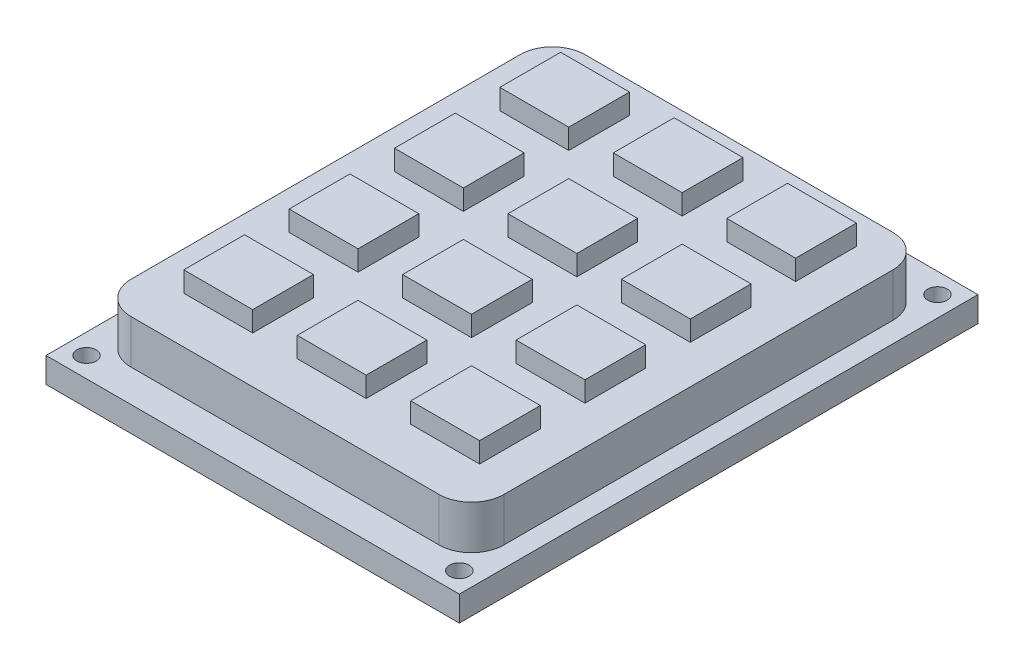
SolidWorks part; units mm, degrees
ref_plane "Front" through (0, 0, 0) normal (0, 0, 1) x (1, 0, 0)
ref_plane "Top" through (0, 0, 0) normal (0, 1, 0) x (1, 0, 0)
ref_plane "Right" through (0, 0, 0) normal (1, 0, 0) x (0, 0, -1)
sketch "Sketch1" plane through (0, 0, 0) normal (0, 1, 0) x (1, 0, 0)
  line L5 (25.5, -32) -> (-25.5, -32)
  line L6 (25.5, -32) -> (25.5, 32)
  line L7 (25.5, 32) -> (-25.5, 32)
  line L8 (-25.5, -32) -> (-25.5, 32)
  line L9 (0, 32) -> (0, -32) construction
  line L10 (25.5, 0) -> (-25.5, 0) construction
extrude "Boss-Extrude1" add sketch "Sketch1" along normal blind 3.1
sketch "Sketch2" plane through (0, 3.1, 0) normal (0, 1, 0) x (1, 0, 0)
  circle A0 centre (-23, 29.5) radius 1.2
  circle A1 centre (23, 29.5) radius 1.2
  circle A2 centre (23, -29.5) radius 1.2
  circle A3 centre (-23, -29.5) radius 1.2
extrude "Cut-Extrude1" cut sketch "Sketch2" against normal blind 3.1
sketch "Sketch3" plane through (0, 3.1, 0) normal (0, 1, 0) x (1, 0, 0)
  line L0 (-19, 28) -> (19, 28)
  line L4 (-23, 24) -> (-23, -24)
  line L14 (-19, -28) -> (19, -28)
  line L16 (23, -24) -> (23, 24)
  arc A0 (-19, -28) -> (-23, -24) centre (-19, -24) cw
  arc A1 (19, -28) -> (23, -24) centre (19, -24) ccw
  arc A2 (-19, 28) -> (-23, 24) centre (-19, 24) ccw
  arc A3 (23, 24) -> (19, 28) centre (19, 24) ccw
extrude "Boss-Extrude2" add sketch "Sketch3" along normal blind 5.4
sketch "Sketch4" plane through (0, 8.5, 0) normal (0, 1, 0) x (1, 0, 0)
  line L4 (-9.75, 16.75) -> (-18.25, 16.75)
  line L5 (-9.75, 16.75) -> (-9.75, 24.25)
  line L6 (-9.75, 24.25) -> (-18.25, 24.25)
  line L7 (-18.25, 16.75) -> (-18.25, 24.25)
  line L12 (4.25, 16.75) -> (-4.25, 16.75)
  line L13 (4.25, 16.75) -> (4.25, 24.25)
  line L14 (4.25, 24.25) -> (-4.25, 24.25)
  line L15 (-4.25, 16.75) -> (-4.25, 24.25)
  line L18 (-9.75, -22.25) -> (-18.25, -22.25)
  line L19 (-9.75, -22.25) -> (-9.75, -14.75)
  line L21 (18.25, 16.75) -> (9.75, 16.75)
  line L22 (18.25, 16.75) -> (18.25, 24.25)
  line L23 (18.25, 24.25) -> (9.75, 24.25)
  line L24 (9.75, 16.75) -> (9.75, 24.25)
  line L29 (9.75, 3.75) -> (18.25, 3.75)
  line L30 (4.25, 3.75) -> (-4.25, 3.75)
  line L31 (9.75, 3.75) -> (9.75, 11.25)
  line L33 (14, 11.25) -> (18.25, 11.25)
  line L34 (9.75, 11.25) -> (18.25, 11.25)
  line L35 (-9.75, -14.75) -> (-18.25, -14.75)
  line L36 (-18.25, -22.25) -> (-18.25, -14.75)
  line L38 (-18.25, -5.5) -> (-18.25, -1.75)
  line L40 (18.25, -5.5) -> (18.25, -1.75)
  line L41 (4.25, 3.75) -> (4.25, 11.25)
  line L42 (-9.75, 3.75) -> (-18.25, 3.75)
  line L43 (-9.75, 3.75) -> (-9.75, 11.25)
  line L44 (-9.75, 11.25) -> (-18.25, 11.25)
  line L45 (-18.25, 3.75) -> (-18.25, 11.25)
  line L48 (4.25, 11.25) -> (-4.25, 11.25)
  line L49 (-4.25, 3.75) -> (-4.25, 11.25)
  line L52 (18.25, 3.75) -> (18.25, 11.25)
  line L57 (4.25, -22.25) -> (-4.25, -22.25)
  line L58 (-9.75, -9.25) -> (-18.25, -9.25)
  line L59 (-9.75, -9.25) -> (-9.75, -1.75)
  line L60 (-9.75, -1.75) -> (-18.25, -1.75)
  line L61 (-18.25, -9.25) -> (-18.25, -1.75)
  line L64 (4.25, -9.25) -> (-4.25, -9.25)
  line L65 (4.25, -9.25) -> (4.25, -1.75)
  line L66 (4.25, -1.75) -> (-4.25, -1.75)
  line L67 (-4.25, -9.25) -> (-4.25, -1.75)
  line L70 (9.75, -9.25) -> (18.25, -9.25)
  line L71 (9.75, -9.25) -> (9.75, -1.75)
  line L72 (9.75, -1.75) -> (18.25, -1.75)
  line L73 (18.25, -9.25) -> (18.25, -1.75)
  line L76 (4.25, -22.25) -> (4.25, -14.75)
  line L77 (4.25, -14.75) -> (-4.25, -14.75)
  line L78 (-4.25, -22.25) -> (-4.25, -14.75)
  line L81 (9.75, -22.25) -> (18.25, -22.25)
  line L82 (9.75, -22.25) -> (9.75, -14.75)
  line L83 (9.75, -14.75) -> (18.25, -14.75)
  line L84 (18.25, -22.25) -> (18.25, -14.75)
extrude "Boss-Extrude4" add sketch "Sketch4" along normal blind 2.5 contours L7 L4 L5 L6 | L15 L12 L13 L14 | L24 L21 L22 L23 | L29 L52 L33 L34 L31 | L49 L30 L41 L48 | L45 L42 L43 L44 | L61 L58 L59 L60 L38 | L67 L64 L65 L66 | L70 L73 L40 L72 L71 | L81 L84 L83 L82 | L78 L57 L76 L77 | L36 L18 L19 L35
